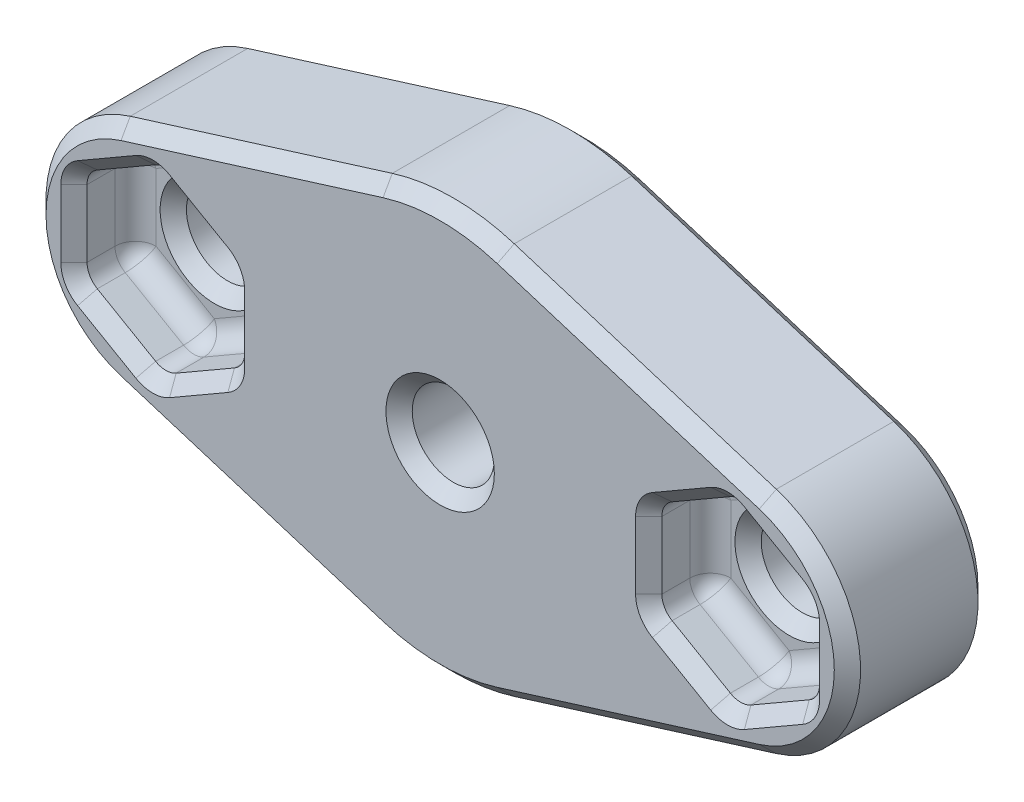
SolidWorks part; units mm, degrees
ref_plane "Front" through (0, 0, 0) normal (0, 0, 1) x (1, 0, 0)
ref_plane "Top" through (0, 0, 0) normal (0, 1, 0) x (1, 0, 0)
ref_plane "Right" through (0, 0, 0) normal (1, 0, 0) x (0, 0, -1)
sketch "Sketch10" plane through (0, 0, 0) normal (0, 0, 1) x (1, 0, 0)
  line L0 (-11.1125, 0) -> (0, 0) construction
  line L1 (0, 0) -> (11.1125, 0) construction
  line L2 (-12.4899, 4.4261) -> (-2.3586, 7.579)
  line L3 (-12.4899, -4.4261) -> (-2.3586, -7.579)
  line L4 (2.3586, -7.579) -> (12.4899, -4.4261)
  line L5 (2.3586, 7.579) -> (12.4899, 4.4261)
  arc A0 (-2.3586, -7.579) -> (2.3586, -7.579) centre (0, 0) ccw
  circle A1 centre (11.1125, 0) radius 3.048 construction
  circle A2 centre (-11.1125, 0) radius 3.048 construction
  circle A3 centre (11.1125, 0) radius 3.175 construction
  arc A4 (12.4899, -4.4261) -> (12.4899, 4.4261) centre (11.1125, 0) ccw
  arc A5 (-6.477, 0) -> (-7.4242, 2.808) centre (-11.1125, 0) ccw construction
  circle A6 centre (0, 0) radius 1.5875
  circle A7 centre (-11.1125, 0) radius 1.5875
  circle A8 centre (11.1125, 0) radius 1.5875
  arc A9 (-7.4242, -2.808) -> (-2.3586, -7.579) centre (0, 0) ccw construction
  arc A10 (-12.4899, -4.4261) -> (-7.4242, -2.808) centre (-11.1125, 0) ccw construction
  arc A11 (-7.9375, 0) -> (-7.4242, -2.808) centre (0, 0) ccw construction
  arc A12 (-7.4242, -2.808) -> (-6.477, 0) centre (-11.1125, 0) ccw construction
  arc A13 (-7.4242, 2.808) -> (-12.4899, 4.4261) centre (-11.1125, 0) ccw construction
  arc A14 (-12.4899, 4.4261) -> (-12.4899, -4.4261) centre (-11.1125, 0) ccw
  arc A15 (-2.3586, 7.579) -> (-7.4242, 2.808) centre (0, 0) ccw construction
  arc A16 (-7.4242, 2.808) -> (-7.9375, 0) centre (0, 0) ccw construction
  arc A17 (7.4242, 2.808) -> (2.3586, 7.579) centre (0, 0) ccw construction
  arc A18 (2.3586, 7.579) -> (-2.3586, 7.579) centre (0, 0) ccw
  arc A19 (12.4899, 4.4261) -> (7.4242, 2.808) centre (11.1125, 0) ccw construction
  arc A20 (7.9375, 0) -> (7.4242, 2.808) centre (0, 0) ccw construction
  arc A21 (7.4242, 2.808) -> (6.477, 0) centre (11.1125, 0) ccw construction
  arc A22 (6.477, 0) -> (7.4242, -2.808) centre (11.1125, 0) ccw construction
  arc A23 (7.4242, -2.808) -> (7.9375, 0) centre (0, 0) ccw construction
  arc A24 (7.4242, -2.808) -> (12.4899, -4.4261) centre (11.1125, 0) ccw construction
  arc A25 (2.3586, -7.579) -> (7.4242, -2.808) centre (0, 0) ccw construction
  point P26 (-12.4896, 4.4261)
  dimension "D1" = 15.875
  dimension "D2" = 6.096
  dimension "D3" = 6.35
  dimension "D4" = 1.5875
  dimension "D5" = 3.175
extrude "Boss-Extrude2" add sketch "Sketch10" along normal blind 5.5562
sketch "Sketch11" plane through (0, 0, 5.5562) normal (0, 0, 1) x (1, 0, 0)
  line L1 (-11.1125, 3.5195) -> (-14.1605, 1.7598)
  line L2 (-14.1605, 1.7598) -> (-14.1605, -1.7598)
  line L3 (-14.1605, -1.7598) -> (-11.1125, -3.5195)
  line L4 (-11.1125, -3.5195) -> (-8.0645, -1.7598)
  line L5 (-8.0645, -1.7598) -> (-8.0645, 1.7598)
  line L6 (-8.0645, 1.7598) -> (-11.1125, 3.5195)
  line L7 (14.1605, 1.7598) -> (11.1125, 3.5195)
  line L8 (11.1125, 3.5195) -> (8.0645, 1.7598)
  line L9 (8.0645, 1.7598) -> (8.0645, -1.7598)
  line L10 (8.0645, -1.7598) -> (11.1125, -3.5195)
  line L11 (11.1125, -3.5195) -> (14.1605, -1.7598)
  line L12 (14.1605, -1.7598) -> (14.1605, 1.7598)
  circle A0 centre (-11.1125, 0) radius 3.048 construction
  circle A1 centre (11.1125, 0) radius 3.048 construction
  dimension "D1" = 6.096
extrude "Cut-Extrude5" cut sketch "Sketch11" against normal blind 2.3813
sketch "Sketch12" plane through (0, 0, 0) normal (0, 0, -1) x (-1, 0, 0)
  line L1 (3.048, 1.7598) -> (0, 3.5195)
  line L2 (0, 3.5195) -> (-3.048, 1.7598)
  line L3 (-3.048, 1.7598) -> (-3.048, -1.7598)
  line L4 (-3.048, -1.7598) -> (0, -3.5195)
  line L5 (0, -3.5195) -> (3.048, -1.7598)
  line L6 (3.048, -1.7598) -> (3.048, 1.7598)
  circle A0 centre (0, 0) radius 3.048 construction
  dimension "D1" = 6.096
extrude "Cut-Extrude6" cut sketch "Sketch12" against normal blind 2.3813
fillet "Fillet2" radius 0.7937 36 edges at (-1.524, 2.6396, 2.3813) (1.524, 2.6396, 2.3813) (3.048, 0, 2.3813) (1.524, -2.6396, 2.3813) (-1.524, -2.6396, 2.3813) (-3.048, 1.7598, 1.1906) (0, 3.5195, 1.1906) (3.048, 1.7598, 1.1906) (3.048, -1.7598, 1.1906) (0, -3.5195, 1.1906) (-3.048, -1.7598, 1.1906) (-3.048, 0, 2.3813) (14.1605, 0, 3.175) (12.6365, 2.6396, 3.175) (9.5885, 2.6396, 3.175) (8.0645, 0, 3.175) (9.5885, -2.6396, 3.175) (12.6365, -2.6396, 3.175) (14.1605, 1.7598, 4.3656) (11.1125, 3.5195, 4.3656) (8.0645, 1.7598, 4.3656) (8.0645, -1.7598, 4.3656) (11.1125, -3.5195, 4.3656) (14.1605, -1.7598, 4.3656) (-9.5885, 2.6396, 3.175) (-12.6365, 2.6396, 3.175) (-14.1605, 0, 3.175) (-12.6365, -2.6396, 3.175) (-9.5885, -2.6396, 3.175) (-8.0645, 0, 3.175) (-11.1125, 3.5195, 4.3656) (-14.1605, 1.7598, 4.3656) (-11.1125, -3.5195, 4.3656) (-8.0645, -1.7598, 4.3656) (-8.0645, 1.7598, 4.3656) (-14.1605, -1.7598, 4.3656)
chamfer "Chamfer2" distance 0.508 angle 45 58 edges at (-1.5875, 0, 2.3813) (-7.4242, -6.0026, 0) (0, -7.9375, 0) (7.4242, -6.0026, 0) (15.748, 0, 0) (7.4242, 6.0026, 0) (0, 7.9375, 0) (-7.4242, 6.0026, 0) (-15.748, 0, 0) (0, 3.3967, 0) (1.524, 2.6396, 0) (2.9417, 1.6984, 0) (3.048, 0, 0) (2.9417, -1.6984, 0) (1.524, -2.6396, 0) (0, -3.3967, 0) (-1.524, -2.6396, 0) (-2.9417, -1.6984, 0) (-3.048, 0, 0) (-2.9417, 1.6984, 0) (-1.524, 2.6396, 0) (-9.525, 0, 3.175) (-9.525, 0, 0) (12.7, 0, 3.175) (12.7, 0, 0) (1.5875, 0, 5.5562) (-7.4242, 6.0026, 5.5562) (0, 7.9375, 5.5562) (7.4242, 6.0026, 5.5562) (15.748, 0, 5.5562) (7.4242, -6.0026, 5.5562) (0, -7.9375, 5.5562) (-7.4242, -6.0026, 5.5562) (-15.748, 0, 5.5562) (14.0542, 1.6984, 5.5562) (12.6365, 2.6396, 5.5562) (11.1125, 3.3967, 5.5562) (9.5885, 2.6396, 5.5562) (8.1708, 1.6984, 5.5562) (8.0645, 0, 5.5562) (8.1708, -1.6984, 5.5562) (9.5885, -2.6396, 5.5562) (11.1125, -3.3967, 5.5562) (12.6365, -2.6396, 5.5562) (14.0542, -1.6984, 5.5562) (14.1605, 0, 5.5562) (-11.1125, 3.3967, 5.5562) (-12.6365, 2.6396, 5.5562) (-14.0542, 1.6984, 5.5562) (-14.1605, 0, 5.5562) (-14.0542, -1.6984, 5.5562) (-12.6365, -2.6396, 5.5562) (-11.1125, -3.3967, 5.5562) (-9.5885, -2.6396, 5.5562) (-8.1708, -1.6984, 5.5562) (-8.0645, 0, 5.5562) (-8.1708, 1.6984, 5.5562) (-9.5885, 2.6396, 5.5562)
